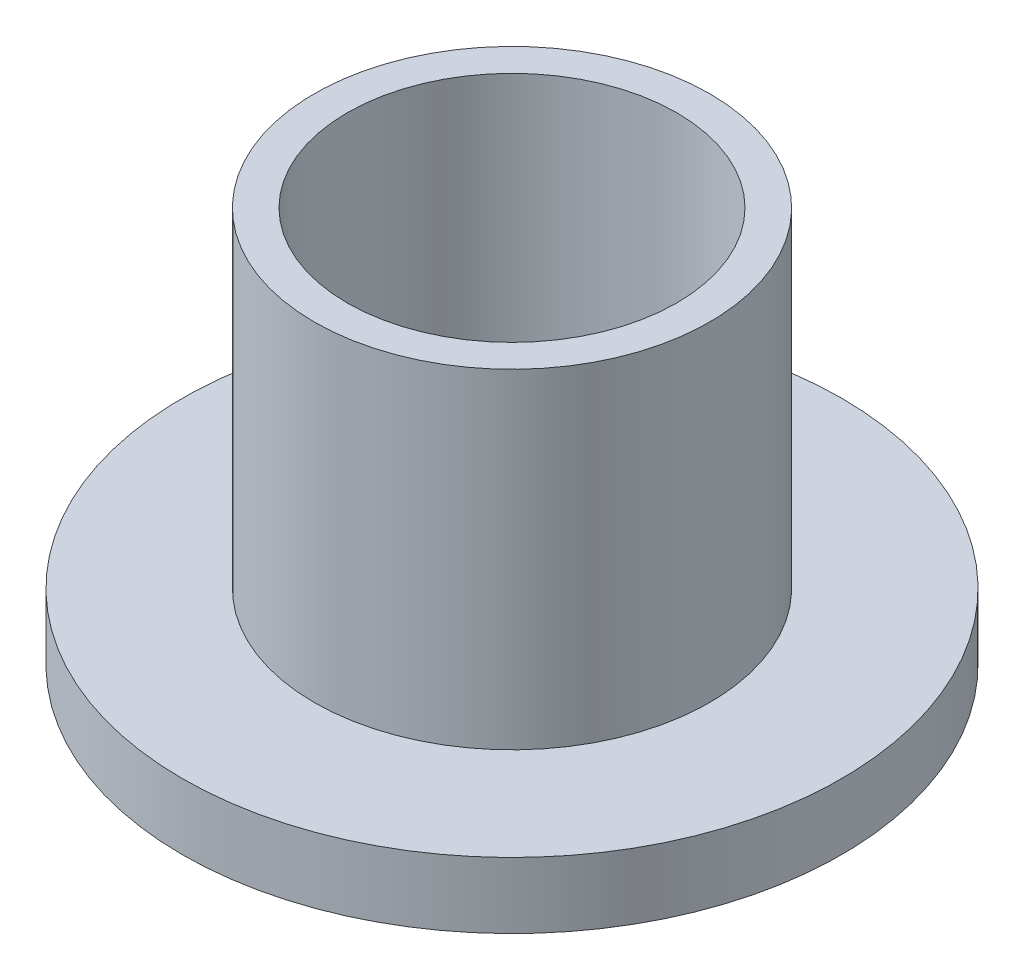
SolidWorks part; units mm, degrees
ref_plane "Front Plane" through (0, 0, 0) normal (0, 0, 1) x (1, 0, 0)
ref_plane "Top Plane" through (0, 0, 0) normal (0, 1, 0) x (1, 0, 0)
ref_plane "Right Plane" through (0, 0, 0) normal (1, 0, 0) x (0, 0, -1)
sketch "Sketch1" plane through (0, 0, 0) normal (0, 1, 0) x (1, 0, 0)
  circle A0 centre (0, 0) radius 10
extrude "Boss-Extrude1" add sketch "Sketch1" along normal blind 2
sketch "Sketch2" plane through (0, 2, 0) normal (0, 1, 0) x (1, 0, 0)
  circle A0 centre (0, 0) radius 6
extrude "Boss-Extrude2" add sketch "Sketch2" along normal blind 10
sketch "Sketch3" plane through (0, 12, 0) normal (0, 1, 0) x (1, 0, 0)
  circle A0 centre (0, 0) radius 5
extrude "Cut-Extrude2" cut sketch "Sketch3" against normal blind 27
